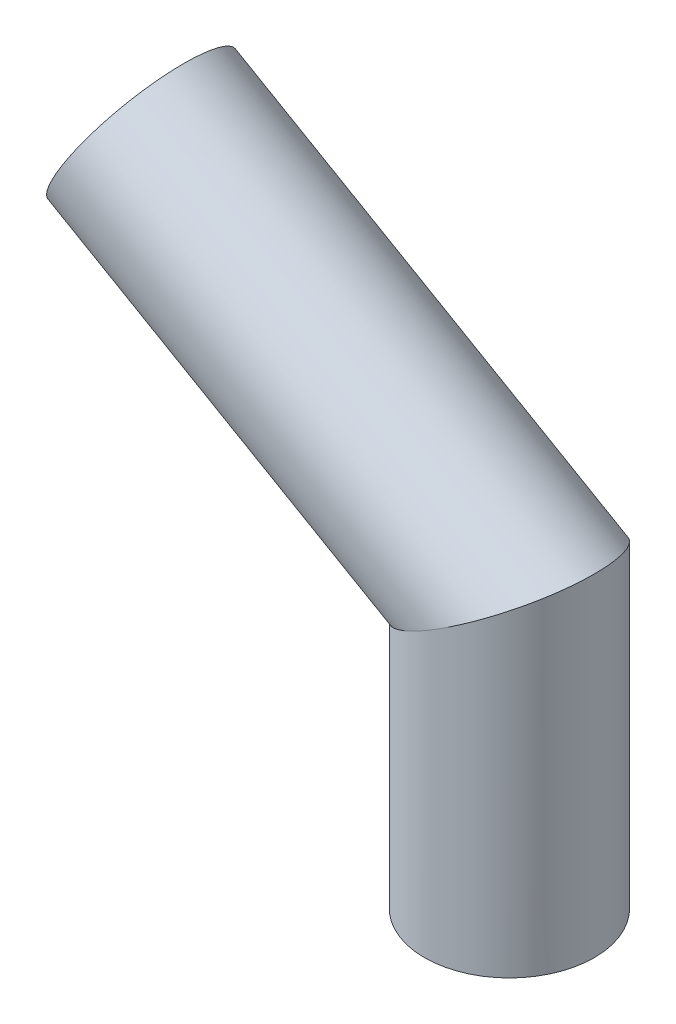
SolidWorks part; units mm, degrees
ref_plane "Front Plane" through (0, 0, 0) normal (0, 0, 1) x (1, 0, 0)
ref_plane "Top Plane" through (0, 0, 0) normal (0, 1, 0) x (1, 0, 0)
ref_plane "Right Plane" through (0, 0, 0) normal (1, 0, 0) x (0, 0, -1)
sketch "Sketch5" plane through (0, 0, 0) normal (0, 0, 1) x (1, 0, 0)
  line L0 (0, 0) -> (1414.8783, 0) construction
  line L1 (0, 0) -> (1299.0381, -750)
  line L2 (1299.0381, -750) -> (1299.0381, -1750)
  dimension "D1" = 1500
  dimension "D2" = 30
  dimension "D3" = 1000
ref_plane "Plane2" through (0, -1750, 0) normal (0, 1, 0) x (1, 0, 0)
sketch "Sketch6" plane through (0, -1750, 0) normal (0, 1, 0) x (1, 0, 0)
  circle A0 centre (1299.0381, 0) radius 299.9773
sweep "Sweep2" add profiles "Sketch6" path "Sketch5"
